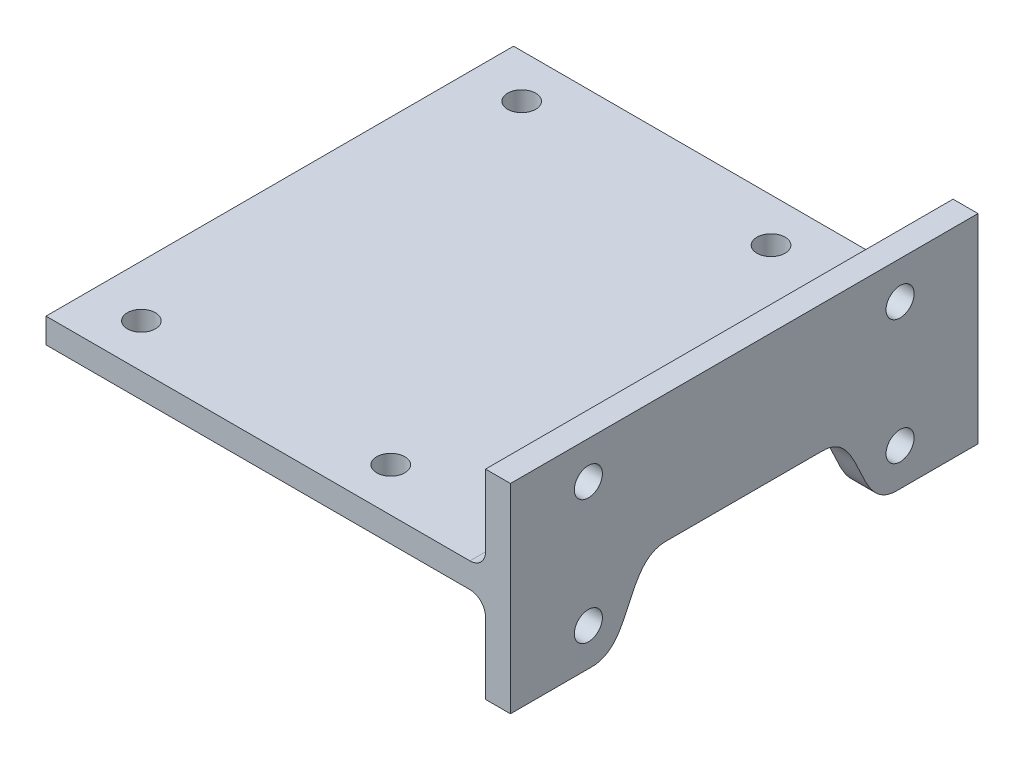
SolidWorks part; units mm, degrees
ref_plane "Front Plane" through (0, 0, 0) normal (0, 0, 1) x (1, 0, 0)
ref_plane "Top Plane" through (0, 0, 0) normal (0, 1, 0) x (1, 0, 0)
ref_plane "Right Plane" through (0, 0, 0) normal (1, 0, 0) x (0, 0, -1)
sketch "Sketch2" plane through (0, 0, 0) normal (0, 0, 1) x (1, 0, 0)
  line L0 (141, 0) -> (141, -28)
  line L1 (0, 0) -> (149, 0)
  line L2 (0, 0) -> (0, 8)
  line L3 (0, 8) -> (149, 8)
  line L4 (149, 0) -> (149, 8)
  line L5 (149, 0) -> (141, 0)
  line L6 (149, 0) -> (149, 36)
  line L7 (149, 36) -> (141, 36)
  line L8 (141, 0) -> (141, 36)
  line L9 (141, -28) -> (149, -28)
  line L10 (149, -28) -> (149, 0)
  dimension "D1" = 8
  dimension "D2" = 149
  dimension "D3" = 28
  dimension "D4" = 28
extrude "Boss-Extrude1" add sketch "Sketch2" along normal blind 150 contours L1 L8 L3 L2 | L8 L1 L4 L3 | L8 L3 L6 L7 | L9 L10 L1 L0
sketch "Sketch3" plane through (0, 0, 0) normal (0, -1, 0) x (1, 0, 0)
  line L1 (96.6, 136) -> (96.6, 150) construction
  line L3 (96.6, 14) -> (96.6, 0) construction
  line L5 (149, 150) -> (149, 0) construction
  line L6 (0, 150) -> (141, 150) construction
  line L7 (0, 0) -> (141, 0) construction
  circle A0 centre (96.6, 136) radius 4.5
  circle A1 centre (16.6, 136) radius 4.5
  circle A2 centre (16.6, 14) radius 4.5
  circle A3 centre (96.6, 14) radius 4.5
  dimension "D1" = 9
  dimension "D3" = 122
  dimension "D2" = 52.4
  dimension "D4" = 80
extrude "Cut-Extrude1" cut sketch "Sketch3" against normal up to next
sketch "Sketch5" plane through (149, 0, 0) normal (1, 0, 0) x (0, 0, -1)
  line L0 (-150, 4) -> (0, 4) construction
  line L1 (-150, -28) -> (-150, 36) construction
  line L2 (0, -28) -> (0, 36) construction
  line L3 (-125, 24) -> (-125, 4) construction
  line L4 (-125, 4) -> (-125, -16) construction
  line L5 (-150, 36) -> (0, 36) construction
  line L6 (-125, 24) -> (-150, 24) construction
  line L7 (-25, 24) -> (0, 24) construction
  circle A0 centre (-125, 24) radius 4.5
  circle A1 centre (-25, 24) radius 4.5
  circle A2 centre (-25, -16) radius 4.5
  circle A3 centre (-125, -16) radius 4.5
  dimension "D1" = 9
  dimension "D2" = 12
  dimension "D3" = 25
extrude "Cut-Extrude2" cut sketch "Sketch5" against normal up to next
fillet "Fillet1" radius 5 2 edges at (141, 0, 75) (141, 8, 75)
sketch "Sketch6" plane through (141, 0, 0) normal (-1, 0, 0) x (0, 0, 1)
  line L0 (150, -28) -> (0, -28) construction
  line L1 (26, -28) -> (0, -28) construction
  line L2 (124, -28) -> (150, -28) construction
  line L3 (150, -5) -> (0, -5) construction
  line L4 (75, -5) -> (75, -28) construction
  line L5 (75, -16.5) -> (38, -16.5) construction
  line L6 (50, -5) -> (100, -5)
  line L7 (124, -28) -> (26, -28)
  line L8 (26, -28) -> (50, -5) construction
  spline S0 degree 3 poles (26, -28) (32.7643, -28) (38, -16.5) (43.2357, -5) (50, -5) knots 0 0 0 0 0.5 1 1 1 1
  spline S1 degree 3 poles (124, -28) (117.2357, -28) (112, -16.5) (106.7643, -5) (100, -5) knots 0 0 0 0 0.5 1 1 1 1
  point P0 (26, -28)
  point P1 (124, -28)
  dimension "D1" = 26
  dimension "D2" = 50
extrude "Cut-Extrude3" cut sketch "Sketch6" against normal up to next
